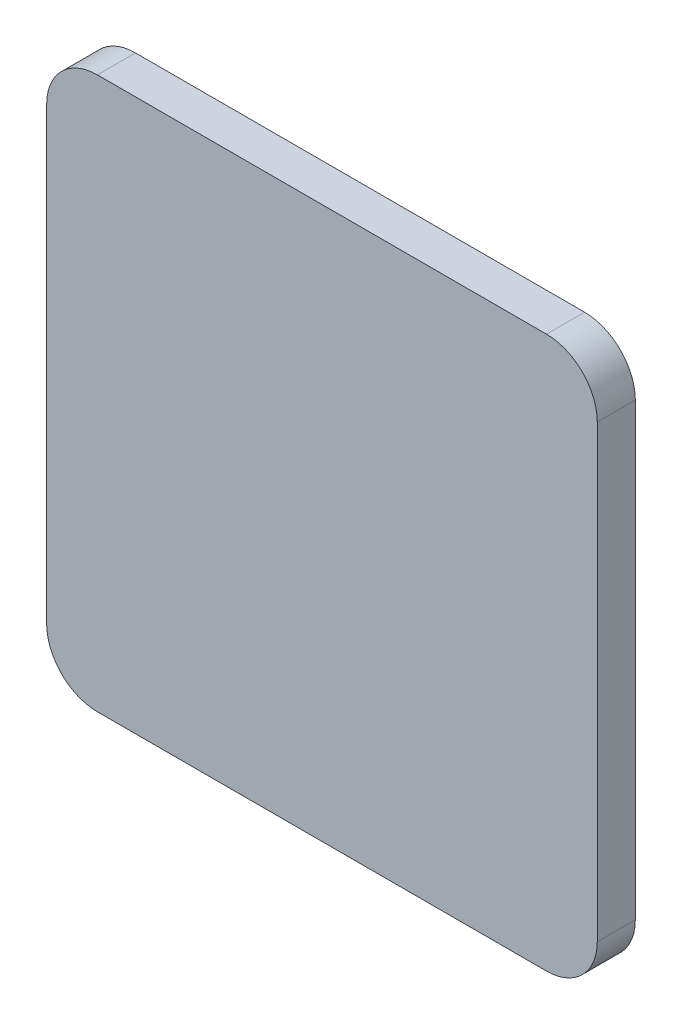
SolidWorks part; units mm, degrees
ref_plane "Front" through (0, 0, 0) normal (0, 0, 1) x (1, 0, 0)
ref_plane "Top" through (0, 0, 0) normal (0, 1, 0) x (1, 0, 0)
ref_plane "Right" through (0, 0, 0) normal (1, 0, 0) x (0, 0, -1)
sketch "Sketch1" plane through (0, 0, 0) normal (0, 0, 1) x (1, 0, 0)
  line L0 (19.7002, 21.7408) -> (2, 21.7408) construction
  line L1 (0, 0) -> (21.7002, 0)
  line L2 (0, 0) -> (0, 21.7408)
  line L3 (0, 21.7408) -> (21.7002, 21.7408)
  line L4 (21.7002, 0) -> (21.7002, 21.7408)
  line L5 (21.7002, 2) -> (21.7002, 19.7408) construction
extrude "Boss-Extrude1" add sketch "Sketch1" along normal blind 1.5
fillet "Fillet1" radius 2 4 edges at (21.7002, 21.7408, 0.75) (0, 21.7408, 0.75) (0, 0, 0.75) (21.7002, 0, 0.75)
